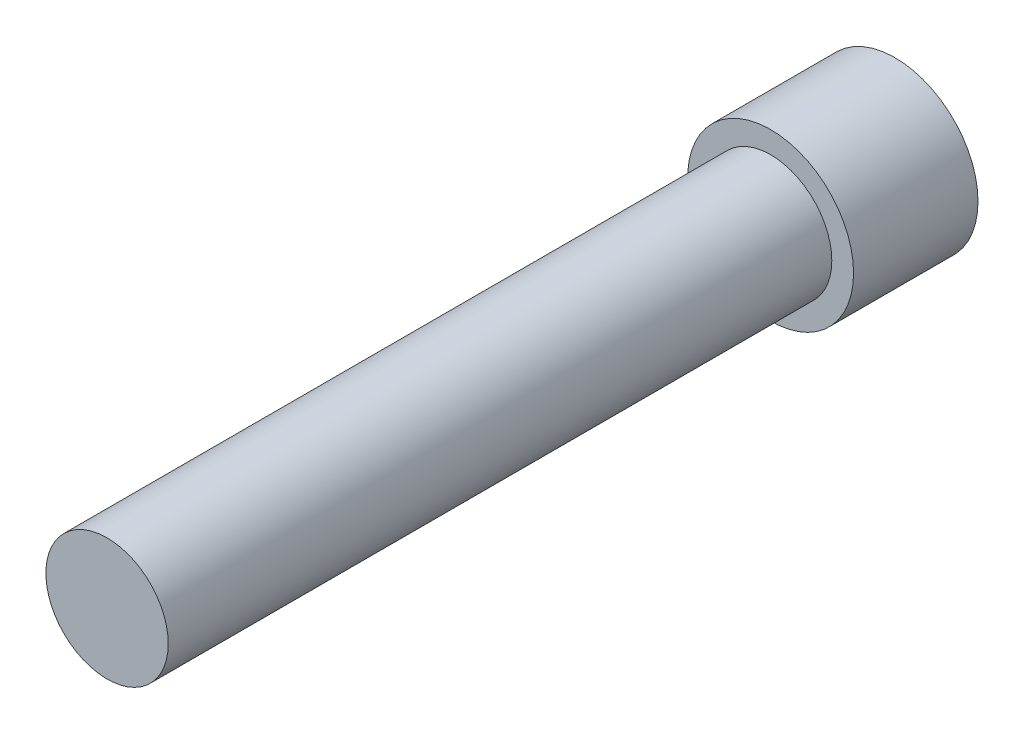
SolidWorks part; units mm, degrees
material "Alloy Steel"
ref_plane "Front Plane" through (0, 0, 0) normal (0, 0, 1) x (1, 0, 0)
ref_plane "Top Plane" through (0, 0, 0) normal (0, 1, 0) x (1, 0, 0)
ref_plane "Right Plane" through (0, 0, 0) normal (1, 0, 0) x (0, 0, -1)
sketch "Sketch1" plane through (0, 0, 0) normal (0, 0, 1) x (1, 0, 0)
  circle A0 centre (0, 0) radius 2
extrude "Extrude1" add sketch "Sketch1" along normal blind 3
sketch "Sketch3" plane through (0, 0, 0) normal (0, 0, -1) x (-1, 0, 0)
  line L1 (-1.4434, 0) -> (-0.7217, -1.25)
  line L2 (-0.7217, -1.25) -> (0.7217, -1.25)
  line L3 (0.7217, -1.25) -> (1.4434, 0)
  line L4 (1.4434, 0) -> (0.7217, 1.25)
  line L5 (0.7217, 1.25) -> (-0.7217, 1.25)
  line L6 (-0.7217, 1.25) -> (-1.4434, 0)
  circle A0 centre (0, 0) radius 1.25 construction
extrude "Extrude3" cut sketch "Sketch3" against normal blind 1.82
sketch "Sketch2" plane through (0, 0, 3) normal (0, 0, 1) x (1, 0, 0)
  circle A0 centre (0, 0) radius 1.475
extrude "Extrude2" add sketch "Sketch2" along normal blind 16
